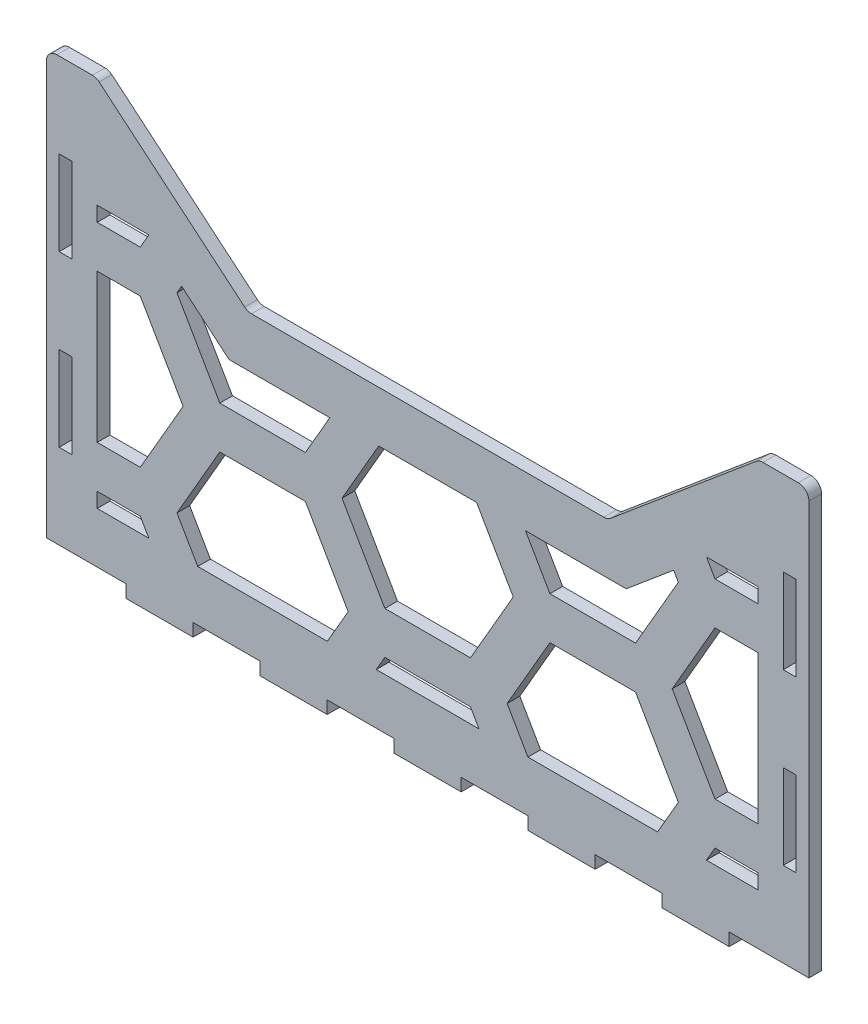
SolidWorks part; units mm, degrees
ref_plane "Front Plane" through (0, 0, 0) normal (0, 0, 1) x (1, 0, 0)
ref_plane "Top Plane" through (0, 0, 0) normal (0, 1, 0) x (1, 0, 0)
ref_plane "Right Plane" through (0, 0, 0) normal (1, 0, 0) x (0, 0, -1)
sketch "Sketch1" plane through (0, 0, 0) normal (0, 0, 1) x (1, 0, 0)
  line L0 (-87, -50) -> (-87, 50) construction
  line L1 (-90, -50) -> (90, -50)
  line L2 (-90, -50) -> (-90, 50)
  line L3 (-90, 50) -> (90, 50)
  line L4 (90, -50) -> (90, 50)
  line L5 (-90, -50) -> (90, 50) construction
  line L6 (-90, 50) -> (90, -50) construction
  line L7 (87, -50) -> (87, 50) construction
  line L8 (-55.3636, -53) -> (-39.5455, -53) construction
  line L9 (-7.9091, -53) -> (7.9091, -53)
  line L10 (-7.9091, -53) -> (-7.9091, -50)
  line L11 (-7.9091, -50) -> (7.9091, -50)
  line L12 (7.9091, -53) -> (7.9091, -50)
  line L13 (-7.9091, -53) -> (7.9091, -50) construction
  line L14 (-7.9091, -50) -> (7.9091, -53) construction
  line L15 (23.7273, -53) -> (39.5455, -53)
  line L16 (23.7273, -53) -> (23.7273, -50)
  line L17 (23.7273, -50) -> (39.5455, -50)
  line L18 (39.5455, -53) -> (39.5455, -50)
  line L19 (23.7273, -53) -> (39.5455, -50) construction
  line L20 (23.7273, -50) -> (39.5455, -53) construction
  line L21 (55.3636, -53) -> (71.1818, -53)
  line L22 (55.3636, -53) -> (55.3636, -50)
  line L23 (55.3636, -50) -> (71.1818, -50)
  line L24 (71.1818, -53) -> (71.1818, -50)
  line L25 (55.3636, -53) -> (71.1818, -50) construction
  line L26 (55.3636, -50) -> (71.1818, -53) construction
  line L27 (-39.5455, -53) -> (-23.7273, -53)
  line L28 (-39.5455, -53) -> (-39.5455, -50)
  line L29 (-39.5455, -50) -> (-23.7273, -50)
  line L30 (-23.7273, -53) -> (-23.7273, -50)
  line L31 (-39.5455, -53) -> (-23.7273, -50) construction
  line L32 (-39.5455, -50) -> (-23.7273, -53) construction
  line L33 (-71.1818, -53) -> (-55.3636, -53)
  line L34 (-71.1818, -53) -> (-71.1818, -50)
  line L35 (-71.1818, -50) -> (-55.3636, -50)
  line L36 (-55.3636, -53) -> (-55.3636, -50)
  line L37 (-71.1818, -53) -> (-55.3636, -50) construction
  line L38 (-71.1818, -50) -> (-55.3636, -53) construction
  line L39 (-23.7273, -53) -> (-7.9091, -53) construction
  line L40 (7.9091, -53) -> (23.7273, -53) construction
  line L41 (39.5455, -53) -> (55.3636, -53) construction
  line L42 (71.1818, -53) -> (87, -53) construction
  line L43 (-71.1818, -53) -> (-87, -53) construction
  line L45 (83.95, 30) -> (87, 30)
  line L46 (83.95, 30) -> (83.95, 10)
  line L47 (83.95, 10) -> (87, 10)
  line L48 (87, 30) -> (87, 10)
  line L49 (83.95, 30) -> (87, 10) construction
  line L50 (83.95, 10) -> (87, 30) construction
  line L63 (83.95, -10) -> (87, -10)
  line L64 (83.95, -10) -> (83.95, -30)
  line L65 (83.95, -30) -> (87, -30)
  line L66 (87, -10) -> (87, -30)
  line L67 (83.95, -10) -> (87, -30) construction
  line L68 (83.95, -30) -> (87, -10) construction
  line L70 (83.95, 50) -> (83.95, 30) construction
  line L71 (83.95, 10) -> (83.95, -10) construction
  line L72 (83.95, -30) -> (83.95, -50) construction
  line L73 (0, -781.5075) -> (0, 49218.4925) construction
  line L82 (-83.95, 10) -> (-87, 10)
  line L83 (-87, 30) -> (-87, 10)
  line L84 (-83.95, 30) -> (-87, 30)
  line L85 (-83.95, 30) -> (-83.95, 10)
  line L86 (-83.95, -30) -> (-87, -30)
  line L87 (-87, -10) -> (-87, -30)
  line L88 (-83.95, -10) -> (-87, -10)
  line L89 (-83.95, -10) -> (-83.95, -30)
  point P0 (0, 0)
  point P10 (0, -51.5)
  point P15 (31.6364, -51.5)
  point P20 (63.2727, -51.5)
  point P25 (-31.6364, -51.5)
  point P30 (-63.2727, -51.5)
  point P39 (85.475, 20)
  point P52 (85.475, -20)
  dimension "D1" = 180
  dimension "D2" = 100
  dimension "D5" = 3
  dimension "D6" = 3.05
  dimension "D3" = 3
  dimension "D4" = 3
extrude "Boss-Extrude1" add sketch "Sketch1" along normal blind 3
sketch "Sketch7" plane through (0, 0, 3) normal (0, 0, 1) x (1, 0, 0)
  line L0 (-78.2526, 50) -> (-42.5, 20)
  line L1 (-90, 50) -> (90, 50) construction
  line L2 (-42.5, 20) -> (42.5, 20)
  line L3 (42.5, 20) -> (78.2526, 50)
  line L4 (-78.2526, 50) -> (78.2526, 50)
  point P4 (0, 20)
  dimension "D1" = 40
  dimension "D2" = 30
  dimension "D3" = 85
extrude "Cut-Extrude9" cut sketch "Sketch7" against normal through all both and the other way through all
fillet "Fillet3" radius 2.5 6 edges at (90, 50, 1.5) (-90, 50, 1.5) (78.2526, 50, 1.5) (42.5, 20, 1.5) (-42.5, 20, 1.5) (-78.2526, 50, 1.5)
sketch "Sketch6" plane through (0, 0, 0) normal (0, 0, 1) x (1, 0, 0)
  line L0 (-145.7809, 10.5) -> (-165.9882, 10.5)
  line L1 (-145.7809, -34.5) -> (-165.9882, -34.5)
  line L2 (-165.9882, -34.5) -> (-176.0918, -52)
  line L3 (-176.0918, -52) -> (-165.9882, -69.5)
  line L4 (-165.9882, -69.5) -> (-145.7809, -69.5)
  line L5 (-145.7809, -69.5) -> (-135.6773, -52)
  line L6 (-135.6773, -52) -> (-145.7809, -34.5)
  line L13 (-165.9882, 10.5) -> (-176.0918, -7)
  line L14 (-137.1207, -74.5) -> (-127.0171, -92)
  line L15 (-127.0171, -92) -> (-106.8098, -92)
  line L16 (-106.8098, -92) -> (-96.7062, -74.5)
  line L17 (-96.7062, -74.5) -> (-106.8098, -57)
  line L18 (-106.8098, -57) -> (-127.0171, -57)
  line L19 (-127.0171, -57) -> (-137.1207, -74.5)
  line L20 (-176.0918, -7) -> (-165.9882, -24.5)
  line L21 (-165.9882, -24.5) -> (-145.7809, -24.5)
  line L22 (-145.7809, -24.5) -> (-135.6773, -7)
  line L23 (-135.6773, -7) -> (-145.7809, 10.5)
  line L24 (-137.1207, -29.5) -> (-127.0171, -47)
  line L25 (-127.0171, -47) -> (-106.8098, -47)
  line L26 (-106.8098, -47) -> (-96.7062, -29.5)
  line L27 (-96.7062, -29.5) -> (-106.8098, -12)
  line L28 (-106.8098, -12) -> (-127.0171, -12)
  line L29 (-127.0171, -12) -> (-137.1207, -29.5)
  line L30 (-145.7809, 55.5) -> (-165.9882, 55.5)
  line L31 (-165.9882, 55.5) -> (-176.0918, 38)
  line L32 (-176.0918, 38) -> (-165.9882, 20.5)
  line L33 (-165.9882, 20.5) -> (-145.7809, 20.5)
  line L34 (-145.7809, 20.5) -> (-135.6773, 38)
  line L35 (-135.6773, 38) -> (-145.7809, 55.5)
  line L36 (-137.1207, 15.5) -> (-127.0171, -2)
  line L37 (-127.0171, -2) -> (-106.8098, -2)
  line L38 (-106.8098, -2) -> (-96.7062, 15.5)
  line L39 (-96.7062, 15.5) -> (-106.8098, 33)
  line L40 (-106.8098, 33) -> (-127.0171, 33)
  line L41 (-127.0171, 33) -> (-137.1207, 15.5)
  line L42 (-145.7809, 100.5) -> (-165.9882, 100.5)
  line L43 (-165.9882, 100.5) -> (-176.0918, 83)
  line L44 (-176.0918, 83) -> (-165.9882, 65.5)
  line L45 (-165.9882, 65.5) -> (-145.7809, 65.5)
  line L46 (-145.7809, 65.5) -> (-135.6773, 83)
  line L47 (-135.6773, 83) -> (-145.7809, 100.5)
  line L48 (-137.1207, 60.5) -> (-127.0171, 43)
  line L49 (-127.0171, 43) -> (-106.8098, 43)
  line L50 (-106.8098, 43) -> (-96.7062, 60.5)
  line L51 (-96.7062, 60.5) -> (-106.8098, 78)
  line L52 (-106.8098, 78) -> (-127.0171, 78)
  line L53 (-127.0171, 78) -> (-137.1207, 60.5)
  line L54 (-145.7809, 145.5) -> (-165.9882, 145.5)
  line L55 (-165.9882, 145.5) -> (-176.0918, 128)
  line L56 (-176.0918, 128) -> (-165.9882, 110.5)
  line L57 (-165.9882, 110.5) -> (-145.7809, 110.5)
  line L58 (-145.7809, 110.5) -> (-135.6773, 128)
  line L59 (-135.6773, 128) -> (-145.7809, 145.5)
  line L60 (-137.1207, 105.5) -> (-127.0171, 88)
  line L61 (-127.0171, 88) -> (-106.8098, 88)
  line L62 (-106.8098, 88) -> (-96.7062, 105.5)
  line L63 (-96.7062, 105.5) -> (-106.8098, 123)
  line L64 (-106.8098, 123) -> (-127.0171, 123)
  line L65 (-127.0171, 123) -> (-137.1207, 105.5)
  line L66 (-145.7809, 190.5) -> (-165.9882, 190.5)
  line L67 (-165.9882, 190.5) -> (-176.0918, 173)
  line L68 (-176.0918, 173) -> (-165.9882, 155.5)
  line L69 (-165.9882, 155.5) -> (-145.7809, 155.5)
  line L70 (-145.7809, 155.5) -> (-135.6773, 173)
  line L71 (-135.6773, 173) -> (-145.7809, 190.5)
  line L72 (-137.1207, 150.5) -> (-127.0171, 133)
  line L73 (-127.0171, 133) -> (-106.8098, 133)
  line L74 (-106.8098, 133) -> (-96.7062, 150.5)
  line L75 (-96.7062, 150.5) -> (-106.8098, 168)
  line L76 (-106.8098, 168) -> (-127.0171, 168)
  line L77 (-127.0171, 168) -> (-137.1207, 150.5)
  line L102 (-145.7809, -34.5) -> (-145.7809, 10.5) construction
  line L103 (-127.0171, -57) -> (-127.0171, -47) construction
  line L104 (-140.7291, -43.25) -> (-132.0689, -38.25) construction
  line L105 (-59.1784, 150.5) -> (-49.0748, 133)
  line L106 (-49.0748, 133) -> (-28.8675, 133)
  line L107 (-28.8675, 133) -> (-18.7639, 150.5)
  line L108 (-18.7639, 150.5) -> (-28.8675, 168)
  line L109 (-28.8675, 168) -> (-49.0748, 168)
  line L110 (-49.0748, 168) -> (-59.1784, 150.5)
  line L111 (-67.8387, 190.5) -> (-88.0459, 190.5)
  line L112 (-88.0459, 190.5) -> (-98.1495, 173)
  line L113 (-98.1495, 173) -> (-88.0459, 155.5)
  line L114 (-88.0459, 155.5) -> (-67.8387, 155.5)
  line L115 (-67.8387, 155.5) -> (-57.735, 173)
  line L116 (-57.735, 173) -> (-67.8387, 190.5)
  line L117 (-67.8387, 145.5) -> (-88.0459, 145.5)
  line L118 (-88.0459, 145.5) -> (-98.1495, 128)
  line L119 (-98.1495, 128) -> (-88.0459, 110.5)
  line L120 (-88.0459, 110.5) -> (-67.8387, 110.5)
  line L121 (-67.8387, 110.5) -> (-57.735, 128)
  line L122 (-57.735, 128) -> (-67.8387, 145.5)
  line L123 (-67.8387, 100.5) -> (-88.0459, 100.5)
  line L124 (-88.0459, 100.5) -> (-98.1495, 83)
  line L125 (-98.1495, 83) -> (-88.0459, 65.5)
  line L126 (-88.0459, 65.5) -> (-67.8387, 65.5)
  line L127 (-67.8387, 65.5) -> (-57.735, 83)
  line L128 (-57.735, 83) -> (-67.8387, 100.5)
  line L129 (-67.8387, 55.5) -> (-88.0459, 55.5)
  line L130 (-88.0459, 55.5) -> (-98.1495, 38)
  line L131 (-98.1495, 38) -> (-88.0459, 20.5)
  line L132 (-88.0459, 20.5) -> (-67.8387, 20.5)
  line L133 (-67.8387, 20.5) -> (-57.735, 38)
  line L134 (-57.735, 38) -> (-67.8387, 55.5)
  line L135 (-59.1784, 15.5) -> (-49.0748, -2)
  line L136 (-49.0748, -2) -> (-28.8675, -2)
  line L137 (-28.8675, -2) -> (-18.7639, 15.5)
  line L138 (-18.7639, 15.5) -> (-28.8675, 33)
  line L139 (-28.8675, 33) -> (-49.0748, 33)
  line L140 (-49.0748, 33) -> (-59.1784, 15.5)
  line L141 (-67.8387, 10.5) -> (-88.0459, 10.5)
  line L142 (-88.0459, 10.5) -> (-98.1495, -7)
  line L143 (-98.1495, -7) -> (-88.0459, -24.5)
  line L144 (-88.0459, -24.5) -> (-67.8387, -24.5)
  line L145 (-67.8387, -24.5) -> (-57.735, -7)
  line L146 (-57.735, -7) -> (-67.8387, 10.5)
  line L147 (-59.1784, -29.5) -> (-49.0748, -47)
  line L148 (-49.0748, -47) -> (-28.8675, -47)
  line L149 (-28.8675, -47) -> (-18.7639, -29.5)
  line L150 (-18.7639, -29.5) -> (-28.8675, -12)
  line L151 (-28.8675, -12) -> (-49.0748, -12)
  line L152 (-49.0748, -12) -> (-59.1784, -29.5)
  line L153 (-67.8387, -34.5) -> (-88.0459, -34.5)
  line L154 (-88.0459, -34.5) -> (-98.1495, -52)
  line L155 (-98.1495, -52) -> (-88.0459, -69.5)
  line L156 (-88.0459, -69.5) -> (-67.8387, -69.5)
  line L157 (-67.8387, -69.5) -> (-57.735, -52)
  line L158 (-57.735, -52) -> (-67.8387, -34.5)
  line L159 (-59.1784, -74.5) -> (-49.0748, -92)
  line L160 (-49.0748, -92) -> (-28.8675, -92)
  line L161 (-28.8675, -92) -> (-18.7639, -74.5)
  line L162 (-18.7639, -74.5) -> (-28.8675, -57)
  line L163 (-28.8675, -57) -> (-49.0748, -57)
  line L164 (-49.0748, -57) -> (-59.1784, -74.5)
  line L165 (-59.1784, 60.5) -> (-49.0748, 43)
  line L166 (-49.0748, 43) -> (-28.8675, 43)
  line L167 (-28.8675, 43) -> (-18.7639, 60.5)
  line L168 (-18.7639, 60.5) -> (-28.8675, 78)
  line L169 (-28.8675, 78) -> (-49.0748, 78)
  line L170 (-49.0748, 78) -> (-59.1784, 60.5)
  line L171 (-59.1784, 105.5) -> (-49.0748, 88)
  line L172 (-49.0748, 88) -> (-28.8675, 88)
  line L173 (-28.8675, 88) -> (-18.7639, 105.5)
  line L174 (-18.7639, 105.5) -> (-28.8675, 123)
  line L175 (-28.8675, 123) -> (-49.0748, 123)
  line L176 (-49.0748, 123) -> (-59.1784, 105.5)
  line L177 (18.7639, 150.5) -> (28.8675, 133)
  line L178 (28.8675, 133) -> (49.0748, 133)
  line L179 (49.0748, 133) -> (59.1784, 150.5)
  line L180 (59.1784, 150.5) -> (49.0748, 168)
  line L181 (49.0748, 168) -> (28.8675, 168)
  line L182 (28.8675, 168) -> (18.7639, 150.5)
  line L183 (10.1036, 190.5) -> (-10.1036, 190.5)
  line L184 (-10.1036, 190.5) -> (-20.2073, 173)
  line L185 (-20.2073, 173) -> (-10.1036, 155.5)
  line L186 (-10.1036, 155.5) -> (10.1036, 155.5)
  line L187 (10.1036, 155.5) -> (20.2073, 173)
  line L188 (20.2073, 173) -> (10.1036, 190.5)
  line L189 (10.1036, 145.5) -> (-10.1036, 145.5)
  line L190 (-10.1036, 145.5) -> (-20.2073, 128)
  line L191 (-20.2073, 128) -> (-10.1036, 110.5)
  line L192 (-10.1036, 110.5) -> (10.1036, 110.5)
  line L193 (10.1036, 110.5) -> (20.2073, 128)
  line L194 (20.2073, 128) -> (10.1036, 145.5)
  line L195 (10.1036, 100.5) -> (-10.1036, 100.5)
  line L196 (-10.1036, 100.5) -> (-20.2073, 83)
  line L197 (-20.2073, 83) -> (-10.1036, 65.5)
  line L198 (-10.1036, 65.5) -> (10.1036, 65.5)
  line L199 (10.1036, 65.5) -> (20.2073, 83)
  line L200 (20.2073, 83) -> (10.1036, 100.5)
  line L201 (10.1036, 55.5) -> (-10.1036, 55.5)
  line L202 (-10.1036, 55.5) -> (-20.2073, 38)
  line L203 (-20.2073, 38) -> (-10.1036, 20.5)
  line L204 (-10.1036, 20.5) -> (10.1036, 20.5)
  line L205 (10.1036, 20.5) -> (20.2073, 38)
  line L206 (20.2073, 38) -> (10.1036, 55.5)
  line L207 (18.7639, 15.5) -> (28.8675, -2)
  line L208 (28.8675, -2) -> (49.0748, -2)
  line L209 (49.0748, -2) -> (59.1784, 15.5)
  line L210 (59.1784, 15.5) -> (49.0748, 33)
  line L211 (49.0748, 33) -> (28.8675, 33)
  line L212 (28.8675, 33) -> (18.7639, 15.5)
  line L213 (10.1036, 10.5) -> (-10.1036, 10.5)
  line L214 (-10.1036, 10.5) -> (-20.2073, -7)
  line L215 (-20.2073, -7) -> (-10.1036, -24.5)
  line L216 (-10.1036, -24.5) -> (10.1036, -24.5)
  line L217 (10.1036, -24.5) -> (20.2073, -7)
  line L218 (20.2073, -7) -> (10.1036, 10.5)
  line L219 (18.7639, -29.5) -> (28.8675, -47)
  line L220 (28.8675, -47) -> (49.0748, -47)
  line L221 (49.0748, -47) -> (59.1784, -29.5)
  line L222 (59.1784, -29.5) -> (49.0748, -12)
  line L223 (49.0748, -12) -> (28.8675, -12)
  line L224 (28.8675, -12) -> (18.7639, -29.5)
  line L225 (10.1036, -34.5) -> (-10.1036, -34.5)
  line L226 (-10.1036, -34.5) -> (-20.2073, -52)
  line L227 (-20.2073, -52) -> (-10.1036, -69.5)
  line L228 (-10.1036, -69.5) -> (10.1036, -69.5)
  line L229 (10.1036, -69.5) -> (20.2073, -52)
  line L230 (20.2073, -52) -> (10.1036, -34.5)
  line L231 (18.7639, -74.5) -> (28.8675, -92)
  line L232 (28.8675, -92) -> (49.0748, -92)
  line L233 (49.0748, -92) -> (59.1784, -74.5)
  line L234 (59.1784, -74.5) -> (49.0748, -57)
  line L235 (49.0748, -57) -> (28.8675, -57)
  line L236 (28.8675, -57) -> (18.7639, -74.5)
  line L237 (18.7639, 60.5) -> (28.8675, 43)
  line L238 (28.8675, 43) -> (49.0748, 43)
  line L239 (49.0748, 43) -> (59.1784, 60.5)
  line L240 (59.1784, 60.5) -> (49.0748, 78)
  line L241 (49.0748, 78) -> (28.8675, 78)
  line L242 (28.8675, 78) -> (18.7639, 60.5)
  line L243 (18.7639, 105.5) -> (28.8675, 88)
  line L244 (28.8675, 88) -> (49.0748, 88)
  line L245 (49.0748, 88) -> (59.1784, 105.5)
  line L246 (59.1784, 105.5) -> (49.0748, 123)
  line L247 (49.0748, 123) -> (28.8675, 123)
  line L248 (28.8675, 123) -> (18.7639, 105.5)
  line L249 (96.7062, 150.5) -> (106.8098, 133)
  line L250 (106.8098, 133) -> (127.0171, 133)
  line L251 (127.0171, 133) -> (137.1207, 150.5)
  line L252 (137.1207, 150.5) -> (127.0171, 168)
  line L253 (127.0171, 168) -> (106.8098, 168)
  line L254 (106.8098, 168) -> (96.7062, 150.5)
  line L255 (88.0459, 190.5) -> (67.8387, 190.5)
  line L256 (67.8387, 190.5) -> (57.735, 173)
  line L257 (57.735, 173) -> (67.8387, 155.5)
  line L258 (67.8387, 155.5) -> (88.0459, 155.5)
  line L259 (88.0459, 155.5) -> (98.1495, 173)
  line L260 (98.1495, 173) -> (88.0459, 190.5)
  line L261 (88.0459, 145.5) -> (67.8387, 145.5)
  line L262 (67.8387, 145.5) -> (57.735, 128)
  line L263 (57.735, 128) -> (67.8387, 110.5)
  line L264 (67.8387, 110.5) -> (88.0459, 110.5)
  line L265 (88.0459, 110.5) -> (98.1495, 128)
  line L266 (98.1495, 128) -> (88.0459, 145.5)
  line L267 (88.0459, 100.5) -> (67.8387, 100.5)
  line L268 (67.8387, 100.5) -> (57.735, 83)
  line L269 (57.735, 83) -> (67.8387, 65.5)
  line L270 (67.8387, 65.5) -> (88.0459, 65.5)
  line L271 (88.0459, 65.5) -> (98.1495, 83)
  line L272 (98.1495, 83) -> (88.0459, 100.5)
  line L273 (88.0459, 55.5) -> (67.8387, 55.5)
  line L274 (67.8387, 55.5) -> (57.735, 38)
  line L275 (57.735, 38) -> (67.8387, 20.5)
  line L276 (67.8387, 20.5) -> (88.0459, 20.5)
  line L277 (88.0459, 20.5) -> (98.1495, 38)
  line L278 (98.1495, 38) -> (88.0459, 55.5)
  line L279 (96.7062, 15.5) -> (106.8098, -2)
  line L280 (106.8098, -2) -> (127.0171, -2)
  line L281 (127.0171, -2) -> (137.1207, 15.5)
  line L282 (137.1207, 15.5) -> (127.0171, 33)
  line L283 (127.0171, 33) -> (106.8098, 33)
  line L284 (106.8098, 33) -> (96.7062, 15.5)
  line L285 (88.0459, 10.5) -> (67.8387, 10.5)
  line L286 (67.8387, 10.5) -> (57.735, -7)
  line L287 (57.735, -7) -> (67.8387, -24.5)
  line L288 (67.8387, -24.5) -> (88.0459, -24.5)
  line L289 (88.0459, -24.5) -> (98.1495, -7)
  line L290 (98.1495, -7) -> (88.0459, 10.5)
  line L291 (96.7062, -29.5) -> (106.8098, -47)
  line L292 (106.8098, -47) -> (127.0171, -47)
  line L293 (127.0171, -47) -> (137.1207, -29.5)
  line L294 (137.1207, -29.5) -> (127.0171, -12)
  line L295 (127.0171, -12) -> (106.8098, -12)
  line L296 (106.8098, -12) -> (96.7062, -29.5)
  line L297 (88.0459, -34.5) -> (67.8387, -34.5)
  line L298 (67.8387, -34.5) -> (57.735, -52)
  line L299 (57.735, -52) -> (67.8387, -69.5)
  line L300 (67.8387, -69.5) -> (88.0459, -69.5)
  line L301 (88.0459, -69.5) -> (98.1495, -52)
  line L302 (98.1495, -52) -> (88.0459, -34.5)
  line L303 (96.7062, -74.5) -> (106.8098, -92)
  line L304 (106.8098, -92) -> (127.0171, -92)
  line L305 (127.0171, -92) -> (137.1207, -74.5)
  line L306 (137.1207, -74.5) -> (127.0171, -57)
  line L307 (127.0171, -57) -> (106.8098, -57)
  line L308 (106.8098, -57) -> (96.7062, -74.5)
  line L309 (96.7062, 60.5) -> (106.8098, 43)
  line L310 (106.8098, 43) -> (127.0171, 43)
  line L311 (127.0171, 43) -> (137.1207, 60.5)
  line L312 (137.1207, 60.5) -> (127.0171, 78)
  line L313 (127.0171, 78) -> (106.8098, 78)
  line L314 (106.8098, 78) -> (96.7062, 60.5)
  line L315 (96.7062, 105.5) -> (106.8098, 88)
  line L316 (106.8098, 88) -> (127.0171, 88)
  line L317 (127.0171, 88) -> (137.1207, 105.5)
  line L318 (137.1207, 105.5) -> (127.0171, 123)
  line L319 (127.0171, 123) -> (106.8098, 123)
  line L320 (106.8098, 123) -> (96.7062, 105.5)
  line L321 (-137.1207, 150.5) -> (-59.1784, 150.5) construction
  line L322 (-93.0977, -43.25) -> (-101.758, -38.25) construction
  line L323 (-46.8676, 8) -> (46.8676, 8)
  line L324 (-78, -38) -> (78, -38)
  line L325 (-78, -38) -> (-78, 24)
  line L326 (-78, 24) -> (78, 24)
  line L327 (78, -38) -> (78, 24)
  line L328 (-78, -38) -> (78, 24) construction
  line L329 (-78, 24) -> (78, -38) construction
  line L330 (-41.5901, 20) -> (41.5901, 20) construction
  line L331 (-106.8098, -12) -> (-78, -12) construction
  line L332 (106.8098, -12) -> (78, -12) construction
  line L333 (46.8676, 8) -> (78, 34.1231)
  line L334 (-46.8676, 8) -> (-78, 34.1231)
  line L335 (-77.5556, 49.4151) -> (-43.197, 20.5849) construction
  line L336 (90, -50) -> (90, 47.5) construction
  line L337 (7.9091, -50) -> (23.7273, -50) construction
  line L338 (43.197, 20.5849) -> (77.5556, 49.4151) construction
  circle A0 centre (-155.8846, -52) radius 17.5 construction
  circle A1 centre (-116.9134, -74.5) radius 17.5 construction
  point P10 (-127.0171, -52)
  point P301 (0, -7)
  point P306 (78, -7)
  point P324 (0, 0)
  point P325 (0, 0)
  point P326 (0, 0)
  point P327 (0, 0)
  point P328 (0, 0)
  point P329 (-9.9552, -27.377)
  point P330 (0, 0)
  point P331 (0, -14.877)
  point P333 (0, 0)
  dimension "D3" = 35
  dimension "D2" = 45
  dimension "D5" = 12
  dimension "D6" = 12
  dimension "D7" = 12
  dimension "D8" = 12
  dimension "D9" = 7
  dimension "D1" = 6
  dimension "D4" = 4
extrude "Cut-Extrude8" cut sketch "Sketch6" against normal through all both and the other way through all contours L325 L144 L145 L146 L141 | L147 L324 L149 L150 L151 L152 | L325 L324 L158 L153 | L226 L324 L230 L225 | L219 L324 L221 L222 L223 L224 | L324 L327 L297 L298 | L288 L327 L285 L286 L287 | L323 L214 L215 L216 L217 L218 | L323 L334 L140 L135 L136 L137 | L333 L323 L207 L208 L209 L210 | L133 L334 L326 L325 L132 | L333 L275 L276 L327 L326
equation "\"bottomLength\"= 270mm"
equation "\"topLength\"= 380mm"
equation "\"frontHeight\"= 100mm"
equation "\"height\"= 180mm"
equation "\"width\"= 180mm"
equation "\"D2@Sketch1\"=\"frontHeight\""
equation "\"D1@Sketch1\"=\"width\""
